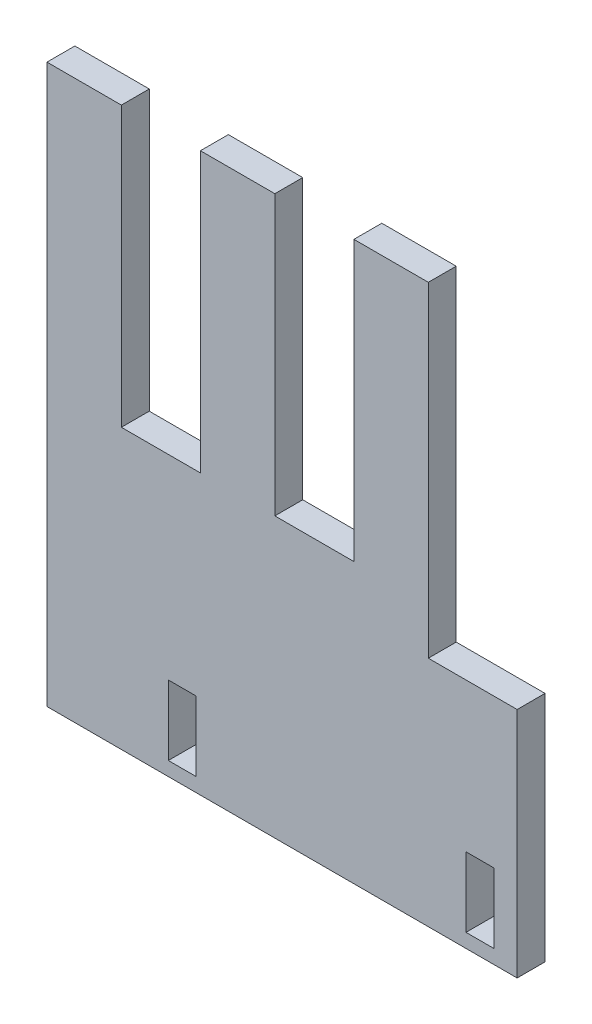
SolidWorks part; units mm, degrees
ref_plane "Plan de face" through (0, 0, 0) normal (0, 0, 1) x (1, 0, 0)
ref_plane "Plan de dessus" through (0, 0, 0) normal (0, 1, 0) x (1, 0, 0)
ref_plane "Plan de droite" through (0, 0, 0) normal (1, 0, 0) x (0, 0, -1)
sketch "Esquisse1" plane through (0, 0, 0) normal (0, 0, 1) x (1, 0, 0)
  line L0 (25.1676, 47.3813) -> (25.1676, -12.6187)
  line L1 (60.2676, -22.6187) -> (41.1676, -22.6187)
  line L2 (-40.8324, 47.3813) -> (-40.8324, -72.6187)
  line L3 (-40.8324, -72.6187) -> (60.2676, -72.6187)
  line L4 (60.2676, -22.6187) -> (60.2676, -72.6187)
  line L5 (55.2676, -54.6187) -> (49.2676, -54.6187)
  line L6 (55.2676, -54.6187) -> (55.2676, -69.6187)
  line L7 (55.2676, -69.6187) -> (49.2676, -69.6187)
  line L8 (49.2676, -54.6187) -> (49.2676, -69.6187)
  line L9 (-8.7324, -54.6187) -> (-14.7324, -54.6187)
  line L10 (-8.7324, -54.6187) -> (-8.7324, -69.6187)
  line L11 (-8.7324, -69.6187) -> (-14.7324, -69.6187)
  line L12 (-14.7324, -54.6187) -> (-14.7324, -69.6187)
  line L13 (25.1676, -12.6187) -> (8.1676, -12.6187)
  line L14 (8.1676, -12.6187) -> (8.1676, 47.3813)
  line L15 (8.1676, 47.3813) -> (-7.8324, 47.3813)
  line L16 (-7.8324, 47.3813) -> (-7.8324, -12.6187)
  line L17 (-7.8324, -12.6187) -> (-24.8324, -12.6187)
  line L18 (-24.8324, -12.6187) -> (-24.8324, 47.3813)
  line L19 (-24.8324, 47.3813) -> (-40.8324, 47.3813)
  line L20 (41.1676, -22.6187) -> (41.1676, 47.3813)
  line L21 (41.1676, 47.3813) -> (25.1676, 47.3813)
  dimension "D1" = 120
  dimension "D2" = 5
  dimension "D3" = 6
  dimension "D4" = 15
  dimension "D5" = 6
  dimension "D6" = 15
  dimension "D7" = 101.1
  dimension "D8" = 3
  dimension "D9" = 16
  dimension "D11" = 58
  dimension "D12" = 17
  dimension "D13" = 16
  dimension "D14" = 17
  dimension "D15" = 16
  dimension "D16" = 60
  dimension "D17" = 60
  dimension "D18" = 60
extrude "Boss.-Extru.1" add sketch "Esquisse1" along normal blind 6
